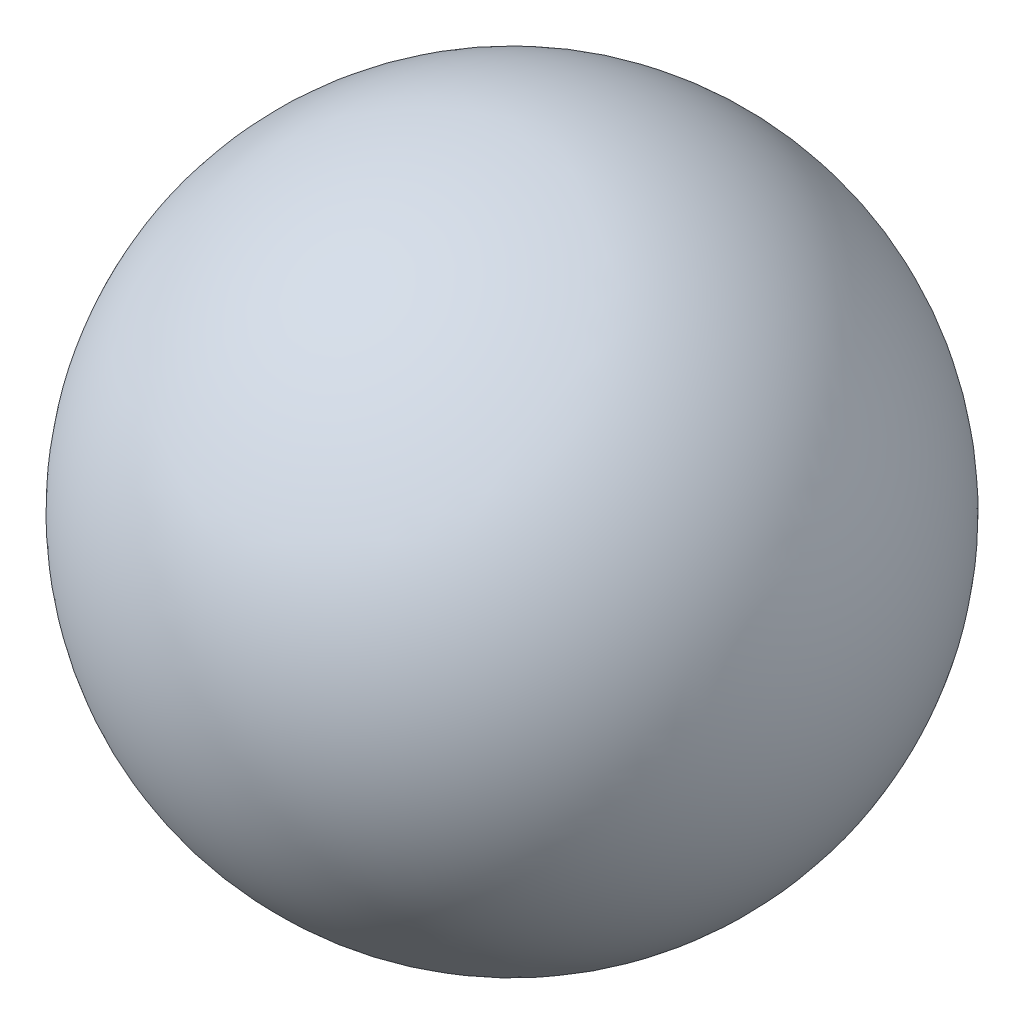
SolidWorks part; units mm, degrees
ref_plane "Front Plane" through (0, 0, 0) normal (0, 0, 1) x (1, 0, 0)
ref_plane "Top Plane" through (0, 0, 0) normal (0, 1, 0) x (1, 0, 0)
ref_plane "Right Plane" through (0, 0, 0) normal (1, 0, 0) x (0, 0, -1)
sketch "Sketch1" plane through (0, 0, 0) normal (0, 1, 0) x (1, 0, 0)
  line L0 (-63.5, 0) -> (63.5, 0) construction
  line L1 (-63.5, 0) -> (63.5, 0)
  arc A0 (-63.5, 0) -> (63.5, 0) centre (0, 0) ccw
  dimension "D1" = 127
revolve "Revolve5" add sketch "Sketch1" angle 360 about L0
